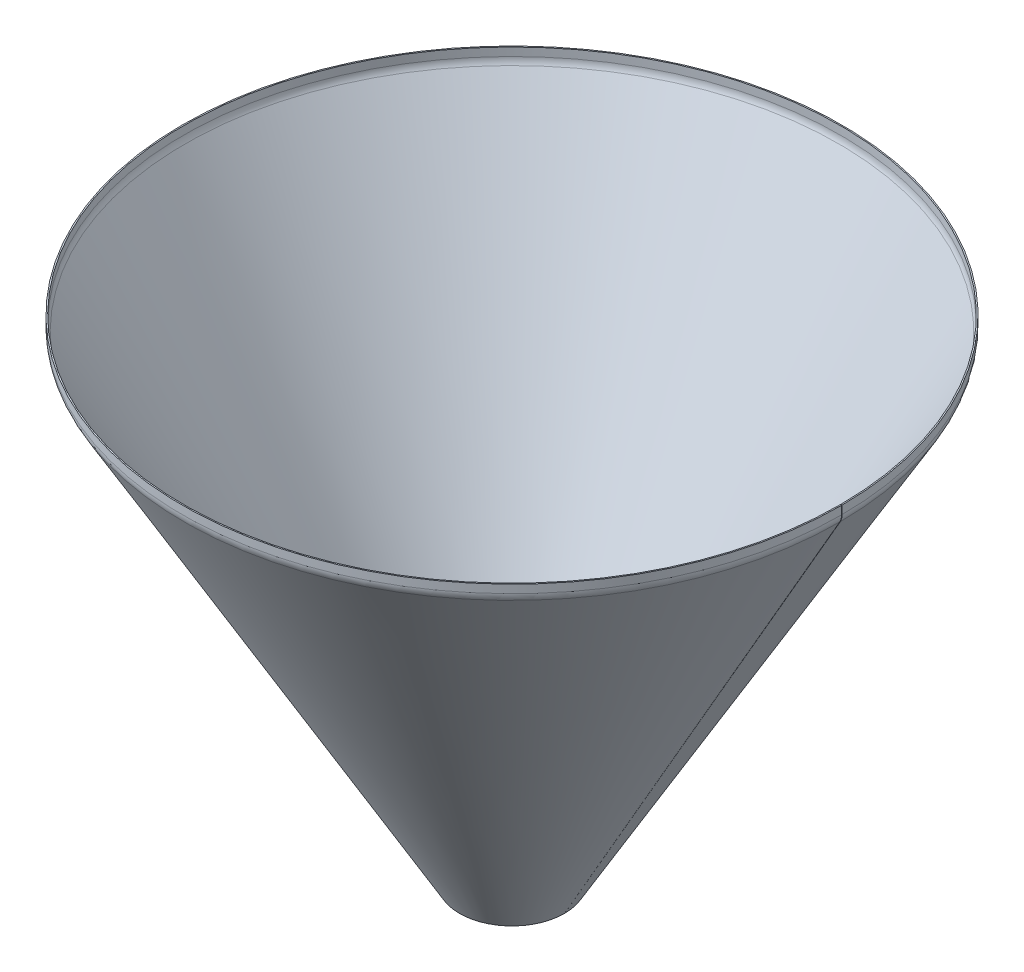
SolidWorks part; units mm, degrees
material "1.4301 (X5CrNi18-10)"
ref_plane "Ebene vorne" through (0, 0, 0) normal (0, 0, 1) x (1, 0, 0)
ref_plane "Ebene oben" through (0, 0, 0) normal (0, 1, 0) x (1, 0, 0)
ref_plane "Ebene rechts" through (0, 0, 0) normal (1, 0, 0) x (0, 0, -1)
sketch "Skizze1" plane through (0, 0, 0) normal (0, 0, 1) x (1, 0, 0)
  line L0 (0, 0) -> (0, -20)
  line L1 (-4.6891, -37.5) -> (-672.5, -1194.1824)
  line L2 (-800, 0) -> (-800, -100.534) construction
  arc A0 (-4.6891, -37.5) -> (0, -20) centre (-35, -20) ccw
  dimension "D1" = 35
  dimension "D2" = 20
  dimension "D3" = 800
  dimension "D4" = 127.5
  dimension "D5" = 150
revolve "Rotation-Dünn4" add sketch "Skizze1" angle 359.9 about L2
sketch "Biegung-Linien3" plane through (0, 0, 0) normal (0, 1, 0) x (1, 0, 0)
sketch "Rahmen3" plane through (0, 0, 0) normal (0, 1, 0) x (1, 0, 0)
